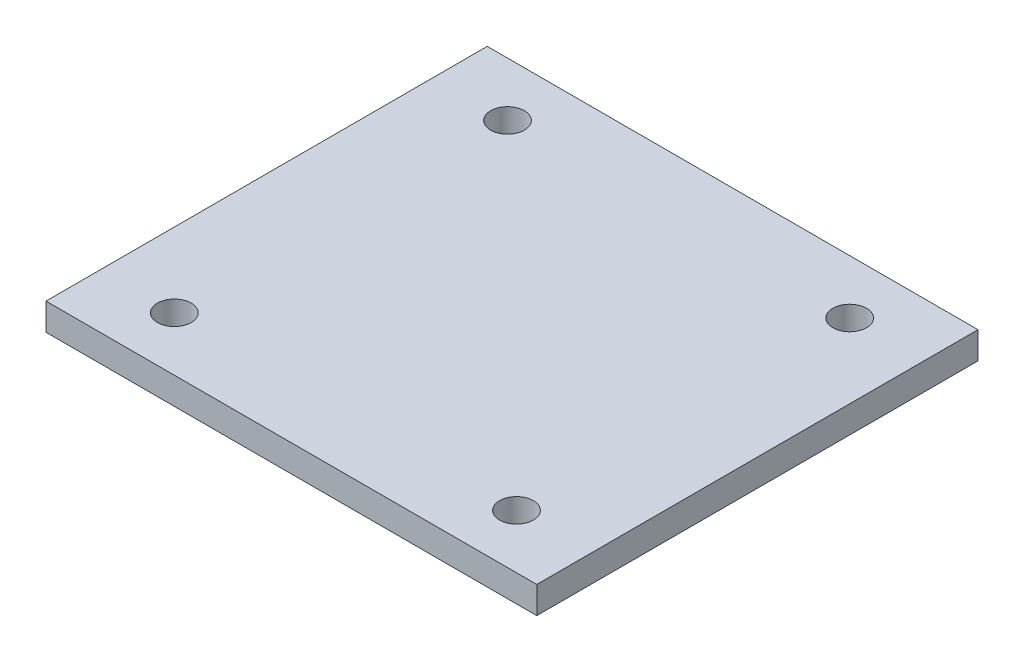
SolidWorks part; units mm, degrees
ref_plane "Plan de face" through (0, 0, 0) normal (0, 0, 1) x (1, 0, 0)
ref_plane "Plan de dessus" through (0, 0, 0) normal (0, 1, 0) x (1, 0, 0)
ref_plane "Plan de droite" through (0, 0, 0) normal (1, 0, 0) x (0, 0, -1)
sketch "Esquisse1" plane through (0, 0, 0) normal (0, 1, 0) x (1, 0, 0)
  line L0 (54.5, 98) -> (54.5, 0) construction
  line L1 (0, 0) -> (109, 0)
  line L2 (0, 0) -> (0, 98)
  line L3 (0, 98) -> (109, 98)
  line L4 (109, 0) -> (109, 98)
  line L5 (0, 49) -> (109, 49) construction
  circle A0 centre (16.5, 86) radius 3.75
  circle A1 centre (92.5, 86) radius 3.75
  circle A2 centre (92.5, 12) radius 3.75
  circle A3 centre (16.5, 12) radius 3.75
  dimension "D3" = 7.5
  dimension "D4" = 7.5
  dimension "D7" = 16.5
  dimension "D1" = 98
  dimension "D2" = 109
  dimension "D5" = 76
  dimension "D6" = 12
extrude "Boss.-Extru.1" add sketch "Esquisse1" along normal blind 6
